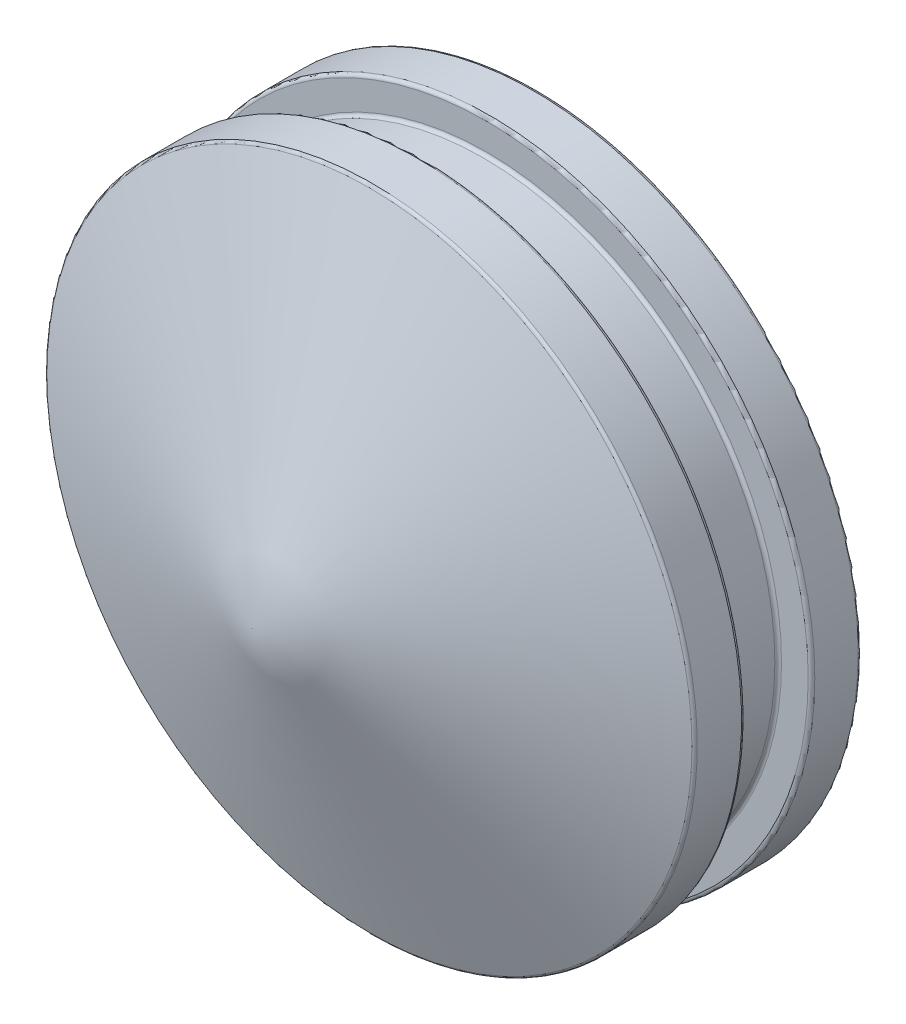
SolidWorks part; units mm, degrees
material "Silicon Rubber"
ref_plane "front" through (0, 0, 0) normal (0, 0, 1) x (1, 0, 0)
ref_plane "top" through (0, 0, 0) normal (0, 1, 0) x (1, 0, 0)
ref_plane "right" through (0, 0, 0) normal (1, 0, 0) x (0, 0, -1)
sketch "Sketch1" plane through (0, 0, 0) normal (0, 1, 0) x (1, 0, 0)
  line L0 (9.75, 3.5487) -> (9.75, 5.0487)
  line L1 (9.75, 5.0487) -> (8.75, 5.0487)
  line L2 (8.75, 5.0487) -> (8.75, 7.0487)
  line L3 (8.75, 7.0487) -> (9.75, 7.0487)
  line L4 (9.75, 7.0487) -> (9.75, 8.5487)
  line L5 (9.75, 8.5487) -> (4, 8.5487)
  line L6 (4, 8.5487) -> (4, 6.0487)
  line L7 (4, 6.0487) -> (5, 6.0487)
  line L8 (5, 6.0487) -> (5, 4.5487)
  line L9 (5, 4.5487) -> (0, 4.5487)
  line L10 (0, -1000) -> (0, 49000) construction
  line L11 (9.75, 3.5487) -> (0, 0)
  line L12 (0, 0) -> (0, 4.5487)
  dimension "D1" = 19.5
  dimension "D2" = 250
  dimension "D3" = 1
  dimension "D4" = 1.5
  dimension "D5" = 2
  dimension "D6" = 5
  dimension "D7" = 8
  dimension "D8" = 2.5
  dimension "D9" = 10
  dimension "D10" = 1.5
revolve "Revolve1" add sketch "Sketch1" angle 360 about L10
fillet "Fillet1" radius 0.1 10 edges at (4, 0, -6.0487) (5, 0, -4.5487) (5, 0, -6.0487) (4, 0, -8.5487) (8.75, 0, -5.0487) (8.75, 0, -7.0487) (9.75, 0, -8.5487) (9.75, 0, -7.0487) (9.75, 0, -5.0487) (9.75, 0, -3.5487)
